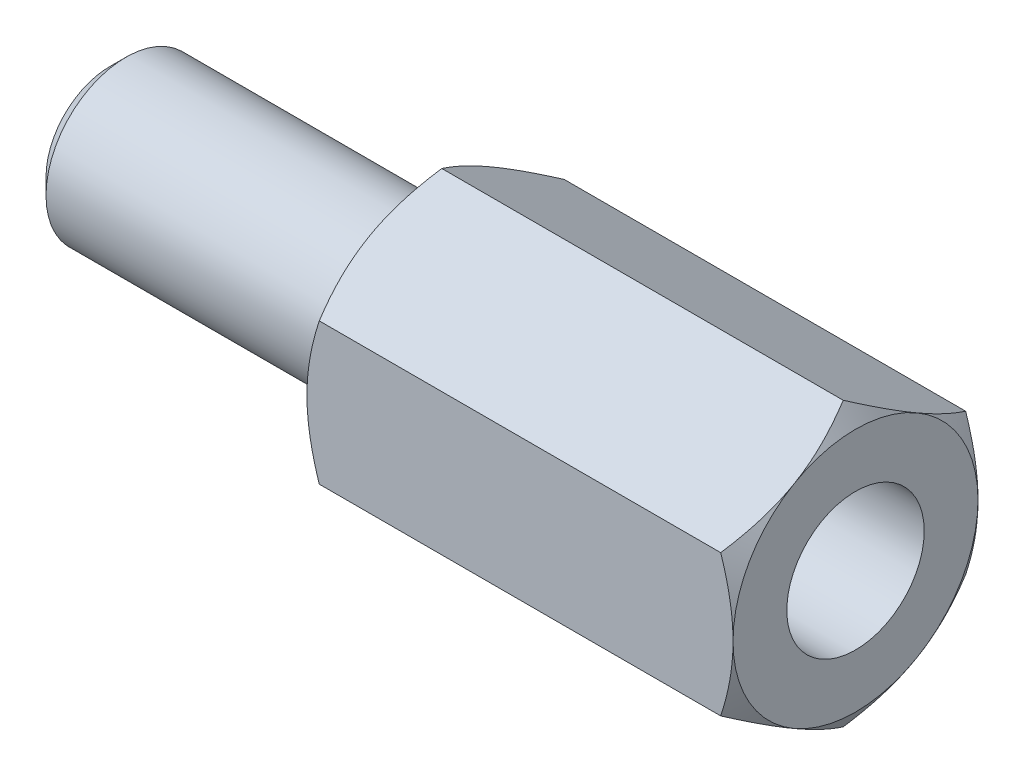
SolidWorks part; units mm, degrees
ref_plane "前视基准面" through (0, 0, 0) normal (0, 0, 1) x (1, 0, 0)
ref_plane "上视基准面" through (0, 0, 0) normal (0, 1, 0) x (1, 0, 0)
ref_plane "右视基准面" through (0, 0, 0) normal (1, 0, 0) x (0, 0, -1)
sketch "草图2" plane through (0, 0, 0) normal (0, 0, 1) x (1, 0, 0)
  line L0 (0, 0) -> (50000, 0) construction
  line L1 (0, 0) -> (0, 1.2)
  line L2 (0.3, 1.5) -> (6, 1.5)
  line L3 (6, 1.5) -> (6, 0)
  line L4 (6, 0) -> (0, 0)
  line L6 (0, 1.2) -> (0.3, 1.5)
  point P4 (0, 1.5)
  dimension "D1" = 6
  dimension "D2" = 3
  dimension "D3" = 0.3
  dimension "D4" = 45
revolve "旋转1" add sketch "草图2" angle 360 about L0
cosmetic thread "装饰螺纹线1" parameters "D2"=2.58
sketch "草图3" plane through (6, 0, 0) normal (1, 0, 0) x (0, 0, -1)
  line L0 (0, 0) -> (0, -50000) construction
  line L2 (0, 2.6558) -> (-2.3, 1.3279)
  line L3 (-2.3, 1.3279) -> (-2.3, -1.3279)
  line L4 (-2.3, -1.3279) -> (0, -2.6558)
  line L5 (0, -2.6558) -> (2.3, -1.3279)
  line L6 (2.3, -1.3279) -> (2.3, 1.3279)
  line L7 (2.3, 1.3279) -> (0, 2.6558)
  circle A0 centre (0, 0) radius 2.3 construction
  dimension "D1" = 4.6
extrude "凸台-拉伸1" add sketch "草图3" along normal blind 8
sketch "草图4" plane through (14, 0, 0) normal (1, 0, 0) x (0, 0, -1)
  circle A0 centre (0, 0) radius 1.29
  dimension "D1" = 2.58
extrude "切除-拉伸1" cut sketch "草图4" against normal blind 4
cosmetic thread "装饰螺纹线2" parameters "D2"=3
sketch "草图5" plane through (10, 0, 0) normal (1, 0, 0) x (0, 0, -1)
  circle A0 centre (0, 0) radius 1.29
  dimension "D1" = 2.58
extrude "切除-拉伸2" cut sketch "草图5" against normal through all draft 60
sketch "草图6" plane through (14, 0, 0) normal (1, 0, 0) x (0, 0, -1)
  line L0 (2.3, 1.3279) -> (0, 2.6558) construction
  circle A0 centre (0, 0) radius 2.3
  circle A1 centre (0, 0) radius 3.45
  dimension "D1" = 6.9
extrude "切除-拉伸3" cut sketch "草图6" against normal through all draft 57
sketch "草图7" plane through (6, 0, 0) normal (-1, 0, 0) x (0, 0, 1)
  line L0 (0, -2.6558) -> (-2.3, -1.3279) construction
  circle A0 centre (0, 0) radius 2.3
  circle A1 centre (0, 0) radius 3.45
  dimension "D1" = 6.9
extrude "切除-拉伸4" cut sketch "草图7" against normal through all draft 57
